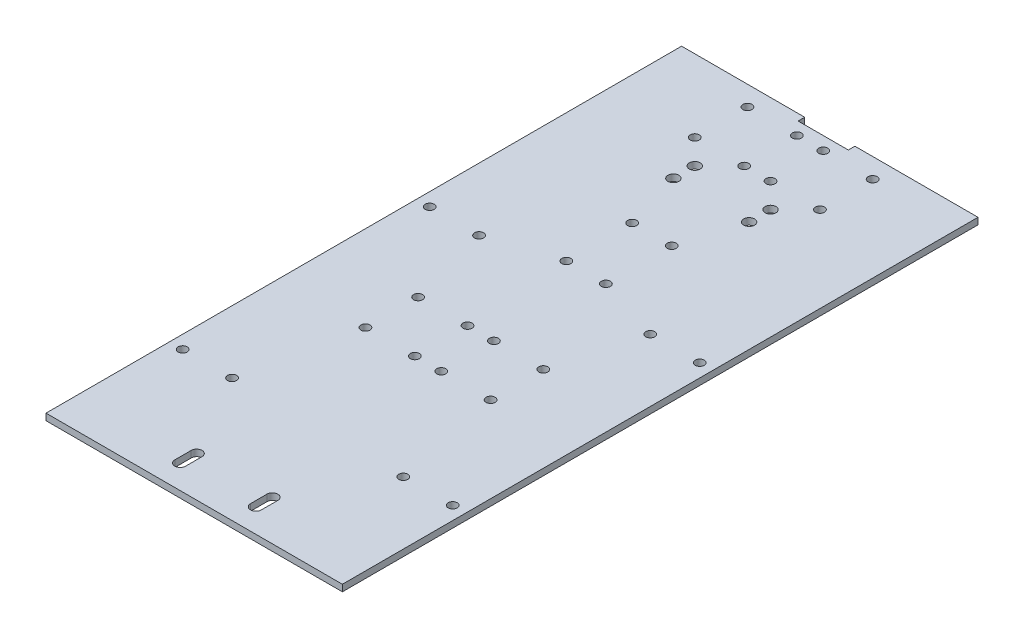
SolidWorks part; units mm, degrees
ref_plane "Спереди" through (0, 0, 0) normal (0, 0, 1) x (1, 0, 0)
ref_plane "Сверху" through (0, 0, 0) normal (0, 1, 0) x (1, 0, 0)
ref_plane "Справа" through (0, 0, 0) normal (1, 0, 0) x (0, 0, -1)
sketch "Эскиз1" plane through (0, 0, 0) normal (0, 1, 0) x (1, 0, 0)
  line L0 (0, 386) -> (74.75, 386)
  line L1 (0, 0) -> (180, 0)
  line L2 (0, 0) -> (0, 386)
  line L4 (180, 0) -> (180, 386)
  line L6 (74.75, 386) -> (74.75, 382)
  line L7 (74.75, 382) -> (105.25, 382)
  line L12 (105.25, 382) -> (105.25, 386)
  line L15 (105.25, 386) -> (180, 386)
  dimension "D1" = 386
  dimension "D2" = 180
  dimension "D3" = 30.5
  dimension "D6" = 4
extrude "Бобышка-Вытянуть1" add sketch "Эскиз1" along normal blind 4
hole_wizard "Диаметр отверстия Ø5.5 (5.5)2" positions "Эскиз2" profile "Эскиз3" hole size "Ø5.5" standard "Ansi Metric" end condition through all
sketch "Эскиз2" plane through (0, 4, 0) normal (0, 1, 0) x (1, 0, 0)
  line L4 (0, 0) -> (180, 0) construction
  line L6 (90, 382) -> (90, 0) construction
  line L10 (105.25, 382) -> (74.75, 382) construction
  line L11 (74.75, 386) -> (0, 386) construction
  line L12 (78, 278) -> (78, 238) construction
  line L13 (52, 374) -> (52, 342) construction
  point P0 (78, 238)
  point P2 (78, 278)
  point P4 (102, 238)
  point P6 (102, 278)
  point P22 (128, 174)
  point P24 (128, 142)
  point P26 (98, 142)
  point P28 (98, 174)
  point P63 (128, 374)
  point P64 (98, 374)
  point P65 (128, 342)
  point P66 (98, 342)
  point P95 (52, 174)
  point P96 (52, 142)
  point P97 (82, 142)
  point P98 (82, 174)
  point P99 (52, 342)
  point P100 (82, 342)
  point P101 (52, 374)
  point P102 (82, 374)
  point P131 (52, 342)
  point P132 (52, 358)
  point P133 (78, 258)
  dimension "D1" = 40
  dimension "D2" = 24
  dimension "D5" = 30
  dimension "D6" = 32
  dimension "D8" = 32
  dimension "D10" = 16
  dimension "D4" = 12
  dimension "D9" = 12
  dimension "D7" = 200
  dimension "D3" = 100
sketch "Эскиз3" plane through (78, 4, -238) normal (1, 0, 0) x (0, 0, 1)
  line L0 (0, 0) -> (0, 4)
  line L1 (0, 4) -> (2.75, 4)
  line L2 (2.75, 4) -> (2.75, 0)
  line L5 (2.75, 0) -> (0, 0)
  line L11 (0, -6.35) -> (0, 107.95) construction
  dimension "Диаметр сквозного отверстия" = 5.5
  dimension "Глубина сквозного отверстия" = 4
hole_wizard "Диаметр отверстия Ø5.5 (5.5)1" positions "Эскиз4" profile "Эскиз5" hole size "Ø5.5" standard "Ansi Metric" end condition through all
sketch "Эскиз4" plane through (0, 4, 0) normal (0, 1, 0) x (1, 0, 0)
  line L2 (0, 0) -> (180, 0) construction
  point P0 (8, 75)
  point P2 (8, 225)
  point P4 (172, 225)
  point P6 (172, 75)
  point P10 (38, 225)
  point P12 (38, 75)
  point P14 (142, 225)
  point P16 (142, 75)
  point P32 (90, 0)
  dimension "D1" = 30
  dimension "D2" = 30
  dimension "D3" = 150
  dimension "D4" = 104
  dimension "D6" = 75
  dimension "D5" = 52
sketch "Эскиз5" plane through (8, 4, -75) normal (1, 0, 0) x (0, 0, 1)
  line L0 (0, 0) -> (0, 4)
  line L1 (0, 4) -> (2.75, 4)
  line L2 (2.75, 4) -> (2.75, 0)
  line L5 (2.75, 0) -> (0, 0)
  line L11 (0, -6.35) -> (0, 107.95) construction
  dimension "Диаметр сквозного отверстия" = 5.5
  dimension "Глубина сквозного отверстия" = 4
hole_wizard "Диаметр отверстия Ø6.6 (6.6)1" positions "Эскиз6" profile "Эскиз7" hole size "Ø6.6" standard "Ansi Metric" end condition through all
sketch "Эскиз6" plane through (0, 4, 0) normal (0, 1, 0) x (1, 0, 0)
  line L1 (0, 0) -> (180, 0) construction
  point P4 (67, 327)
  point P6 (113, 327)
  point P8 (67, 314)
  point P10 (113, 314)
  point P25 (90, 0)
  dimension "D1" = 13
  dimension "D2" = 46
  dimension "D4" = 327
  dimension "D3" = 23
sketch "Эскиз7" plane through (67, 4, -327) normal (1, 0, 0) x (0, 0, 1)
  line L0 (0, 0) -> (0, 4)
  line L1 (0, 4) -> (3.3, 4)
  line L2 (3.3, 4) -> (3.3, 0)
  line L5 (3.3, 0) -> (0, 0)
  line L11 (0, -6.35) -> (0, 107.95) construction
  dimension "Диаметр сквозного отверстия" = 6.6
  dimension "Глубина сквозного отверстия" = 4
sketch "Эскиз8" plane through (0, 4, 0) normal (0, 1, 0) x (1, 0, 0)
  line L0 (67, 24.5) -> (67, 14.5) construction
  line L1 (70.3, 24.5) -> (70.3, 14.5)
  line L2 (63.7, 24.5) -> (63.7, 14.5)
  line L3 (113, 14.5) -> (113, 24.5) construction
  line L4 (109.7, 14.5) -> (109.7, 24.5)
  line L5 (116.3, 14.5) -> (116.3, 24.5)
  arc A0 (70.3, 24.5) -> (63.7, 24.5) centre (67, 24.5) ccw
  arc A1 (63.7, 14.5) -> (70.3, 14.5) centre (67, 14.5) ccw
  arc A2 (109.7, 14.5) -> (116.3, 14.5) centre (113, 14.5) ccw
  arc A3 (116.3, 24.5) -> (109.7, 24.5) centre (113, 24.5) ccw
  point P2 (67, 19.5)
  point P7 (113, 19.5)
  point P14 (67, 314)
  point P15 (113, 314)
  dimension "D1" = 6.6
  dimension "D2" = 10
  dimension "D3" = 294.5
extrude "Вырез-Вытянуть1" cut sketch "Эскиз8" against normal through all
equation "\"D8@Эскиз2\"=\"D6@Эскиз2\""
equation "\"D4@Эскиз2\"=\"D2@Эскиз2\"/2"
equation "\"D2@Эскиз4\"=\"D1@Эскиз4\""
equation "\"D5@Эскиз4\"=\"D4@Эскиз4\"/2"
equation "\"D3@Эскиз6\"=\"D2@Эскиз6\"/2"
equation "\"D3@Эскиз2\"=\"D7@Эскиз2\"/2"
